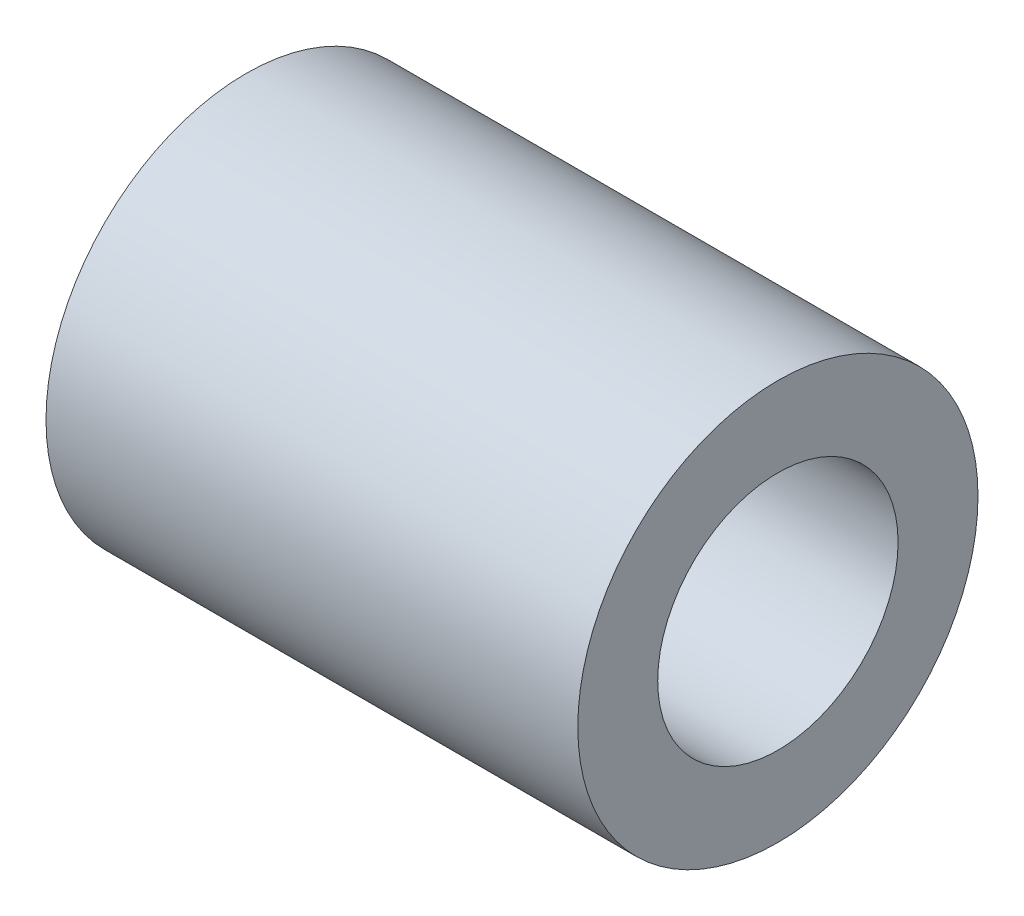
SolidWorks part; units mm, degrees
material "BUTYL"
ref_plane "Alzado" through (0, 0, 0) normal (0, 0, 1) x (1, 0, 0)
ref_plane "Planta" through (0, 0, 0) normal (0, 1, 0) x (1, 0, 0)
ref_plane "Vista lateral" through (0, 0, 0) normal (1, 0, 0) x (0, 0, -1)
sketch "Croquis1" plane through (0, 0, 0) normal (1, 0, 0) x (0, 0, -1)
  circle A0 centre (0, 0) radius 13.32
  circle A1 centre (0, 0) radius 8
  dimension "D1" = 16
  dimension "D2" = 26.64
extrude "Saliente-Extruir1" add sketch "Croquis1" along normal blind 35.4
